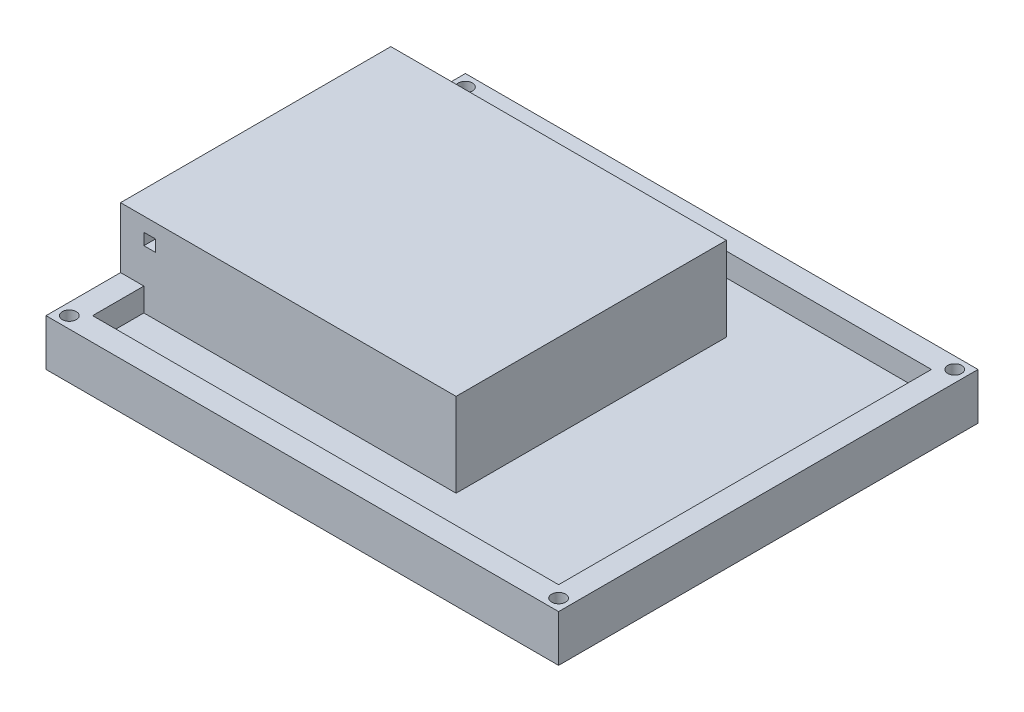
SolidWorks part; units mm, degrees
ref_plane "Front Plane" through (0, 0, 0) normal (0, 0, 1) x (1, 0, 0)
ref_plane "Top Plane" through (0, 0, 0) normal (0, 1, 0) x (1, 0, 0)
ref_plane "Right Plane" through (0, 0, 0) normal (1, 0, 0) x (0, 0, -1)
sketch "Sketch1" plane through (0, 0, 0) normal (0, 1, 0) x (1, 0, 0)
  line L1 (-55, -45) -> (55, -45)
  line L2 (-55, -45) -> (-55, 45)
  line L3 (-55, 45) -> (55, 45)
  line L4 (55, -45) -> (55, 45)
  line L5 (-55, -45) -> (55, 45) construction
  line L6 (-55, 45) -> (55, -45) construction
  point P0 (0, 0)
  dimension "D1" = 110
  dimension "D2" = 90
extrude "Boss-Extrude2" add sketch "Sketch1" along normal blind 5
sketch "Sketch2" plane through (0, 5, 0) normal (0, 1, 0) x (1, 0, 0)
  line L0 (-55, 45) -> (55, 45)
  line L1 (-55, 45) -> (-55, 40)
  line L2 (55, 45) -> (55, 40)
  line L3 (-55, 40) -> (55, 40)
  dimension "D1" = 5
extrude "Boss-Extrude4" add sketch "Sketch2" along normal blind 25
sketch "Sketch3" plane through (0, 5, 0) normal (0, 1, 0) x (1, 0, 0)
  line L0 (-55, -45) -> (55, -45)
  line L1 (-55, -45) -> (-55, -40)
  line L2 (55, -45) -> (55, -40)
  line L3 (-55, -40) -> (55, -40)
  dimension "D1" = 5
extrude "Boss-Extrude5" add sketch "Sketch3" along normal blind 25
sketch "Sketch5" plane through (0, 5, 0) normal (0, 1, 0) x (1, 0, 0)
  line L0 (55, 40) -> (55, -40)
  line L1 (55, 40) -> (50, 40)
  line L2 (55, -40) -> (50, -40)
  line L3 (50, 40) -> (50, -40)
  line L4 (55, -40) -> (55, 40) construction
  line L5 (55, 40) -> (55, 45) construction
  dimension "D1" = 5
extrude "Boss-Extrude6" add sketch "Sketch5" along normal blind 25
sketch "Sketch7" plane through (0, 5, 0) normal (0, 1, 0) x (1, 0, 0)
sketch "Sketch8" plane through (0, 5, 0) normal (0, 1, 0) x (1, 0, 0)
  line L0 (-55, 29) -> (17, 29)
  line L1 (-55, 40) -> (-55, -40) construction
  line L2 (17, 29) -> (17, -29)
  line L3 (17, -29) -> (-55, -29)
  line L4 (-55, -29) -> (-55, -40)
  line L5 (-55, 40) -> (-55, 29)
  line L6 (-55, 29) -> (17, 29)
  line L7 (-55, 29) -> (-55, -29)
  line L8 (17, 29) -> (17, -29)
  line L9 (-55, -29) -> (17, -29)
  line M3 (-55, 40) -> (-55, -40)
  dimension "D1" = 11
  dimension "D2" = 11
  dimension "D3" = 72
extrude "Boss-Extrude7" add sketch "Sketch8" along normal blind 25 contours L3 L2 L0 M3
sketch "Sketch10" plane through (-55, 0, 0) normal (-1, 0, 0) x (0, 0, 1)
  line L1 (-29, 5) -> (-29, 20.1155)
  line L2 (29, 5) -> (29, 20.1155)
  line L3 (-29, 20.1155) -> (29, 20.1155)
  line L4 (-29, 20.1155) -> (-29, 0)
  line L5 (-29, 20.1155) -> (-26, 20.1155)
  line L6 (-29, 0) -> (-26, 0)
  line L7 (-26, 20.1155) -> (-26, 0)
  line L8 (-45, 0) -> (45, 0) construction
  line L9 (29, 20.1155) -> (29, 0)
  line L10 (29, 20.1155) -> (26, 20.1155)
  line L11 (29, 0) -> (26, 0)
  line L12 (26, 20.1155) -> (26, 0)
  line L13 (-29, 20.1155) -> (29, 20.1155)
  line L14 (-29, 20.1155) -> (-29, 23.1155)
  line L15 (29, 20.1155) -> (29, 23.1155)
  line L16 (-29, 23.1155) -> (29, 23.1155)
  line L17 (-26, 20.1155) -> (26, 20.1155)
  line L18 (-26, 20.1155) -> (-26, 0)
  line L19 (26, 20.1155) -> (26, 0)
  line L20 (-26, 0) -> (26, 0)
  line M22 (-45, 0) -> (45, 0)
  dimension "D1" = 3
  dimension "D2" = 3
  dimension "D3" = 3
extrude "Cut-Extrude1" cut sketch "Sketch10" against normal blind 70 contours L12 L3 L7 M22
sketch "Sketch11" plane through (-55, 0, 0) normal (-1, 0, 0) x (0, 0, 1)
  line L0 (-45, 30) -> (45, 30)
  line L1 (-45, 30) -> (-45, 23)
  line L2 (45, 30) -> (45, 23)
  line L3 (-45, 23) -> (45, 23)
  dimension "D1" = 7
extrude "Cut-Extrude2" cut sketch "Sketch11" against normal blind 110
sketch "Sketch12" plane through (0, 23, 0) normal (0, 1, 0) x (1, 0, 0)
  circle A0 centre (52.5, -42.5) radius 1.5
extrude "Cut-Extrude3" cut sketch "Sketch12" against normal blind 23
sketch "Sketch13" plane through (0, 23, 0) normal (0, 1, 0) x (1, 0, 0)
  circle A0 centre (-52.5, -42.5) radius 1.5
extrude "Cut-Extrude4" cut sketch "Sketch13" against normal blind 23
sketch "Sketch14" plane through (0, 23, 0) normal (0, 1, 0) x (1, 0, 0)
  circle A0 centre (52.5, 42.5) radius 1.5
extrude "Cut-Extrude5" cut sketch "Sketch14" against normal blind 23
sketch "Sketch15" plane through (0, 23, 0) normal (0, 1, 0) x (1, 0, 0)
  circle A0 centre (-52.5, 42.5) radius 1.5
extrude "Cut-Extrude6" cut sketch "Sketch15" against normal blind 23
sketch "Sketch18" plane through (-55, 0, 0) normal (-1, 0, 0) x (0, 0, 1)
  line L0 (-45, 23) -> (-40, 23)
  line L1 (-45, 23) -> (-45, 10)
  line L2 (-40, 23) -> (-40, 10)
  line L3 (-45, 10) -> (-40, 10)
  dimension "D1" = 13
extrude "Cut-Extrude7" cut sketch "Sketch18" against normal blind 110
sketch "Sketch19" plane through (0, 0, -40) normal (0, 0, -1) x (-1, 0, 0)
  line L0 (-55, 23) -> (-50, 23)
  line L1 (-55, 23) -> (-55, 10)
  line L2 (-50, 23) -> (-50, 10)
  line L3 (-55, 10) -> (-50, 10)
  dimension "D1" = 13
extrude "Cut-Extrude13" cut sketch "Sketch19" against normal blind 85
sketch "Sketch26" plane through (50, 0, 0) normal (1, 0, 0) x (0, 0, -1)
  line L0 (-45, 10) -> (-40, 10)
  line L1 (-45, 10) -> (-45, 23)
  line L2 (-40, 10) -> (-40, 23)
  line L3 (-45, 23) -> (-40, 23)
  dimension "D1" = 13
extrude "Cut-Extrude17" cut sketch "Sketch26" against normal blind 105
sketch "Sketch29" plane through (0, 5, 0) normal (0, 1, 0) x (1, 0, 0)
  line L0 (-55, 40) -> (50, 40) construction
  line L1 (-50, 40) -> (-55, 40)
  line L2 (-50, 40) -> (-50, 29)
  line L3 (-50, 29) -> (-55, 29)
  line L4 (-55, 40) -> (-55, 29)
  dimension "D1" = 5
extrude "Boss-Extrude14" add sketch "Sketch29" along normal blind 5
sketch "Sketch30" plane through (0, 5, 0) normal (0, 1, 0) x (1, 0, 0)
  line L0 (17, -29) -> (-55, -29) construction
  line L1 (-50, -29) -> (-55, -29)
  line L2 (-50, -29) -> (-50, -40)
  line L3 (-50, -40) -> (-55, -40)
  line L4 (-55, -29) -> (-55, -40)
  dimension "D1" = 5
extrude "Boss-Extrude15" add sketch "Sketch30" along normal blind 5
sketch "Sketch34" plane through (0, 0, 29) normal (0, 0, 1) x (1, 0, 0)
  line L0 (-50, 10) -> (-55, 10)
  line L1 (-50, 10) -> (-50, 20)
  line L2 (-55, 10) -> (-55, 20)
  line L3 (-50, 20) -> (-55, 20)
  line L6 (-50, 20) -> (-47.5, 20)
  line L7 (-50, 20) -> (-50, 17.5)
  line L8 (-50, 17.5) -> (-47.5, 17.5)
  line L9 (-47.5, 20) -> (-47.5, 17.5)
  dimension "D1" = 10
  dimension "D2" = 2.5
  dimension "D3" = 2.5
extrude "Cut-Extrude18" cut sketch "Sketch34" against normal blind 3 contours L9 L6 L1 L8
sketch "Sketch37" plane through (0, 0, 29) normal (0, 0, 1) x (1, 0, 0)
  line L0 (-55, 23) -> (-55, 10)
  line L1 (-55, 23) -> (17, 23)
  line L2 (-55, 10) -> (17, 10)
  line L3 (17, 23) -> (17, 10)
  dimension "D1" = 72
extrude "Cut-Extrude20" cut sketch "Sketch37" against normal blind 58
sketch "Sketch39" plane through (0, 10, 0) normal (0, 1, 0) x (1, 0, 0)
  line L1 (17, 29) -> (-55, 29)
  line L2 (17, 29) -> (17, 26)
  line L3 (17, 26) -> (-55, 26)
  line L4 (-55, 29) -> (-55, 26)
extrude "Boss-Extrude17" add sketch "Sketch39" along normal blind 13
sketch "Sketch41" plane through (0, 10, 0) normal (0, 1, 0) x (1, 0, 0)
  line L1 (15, 26) -> (17, 26)
  line L2 (15, 26) -> (15, -29)
  line L3 (15, -29) -> (17, -29)
  line L4 (17, 26) -> (17, -29)
extrude "Boss-Extrude18" add sketch "Sketch41" along normal blind 13
sketch "Sketch43" plane through (0, 10, 0) normal (0, 1, 0) x (1, 0, 0)
  line L0 (-55, -45) -> (-55, -26) construction
  line L1 (15, -26) -> (-55, -26)
  line L2 (15, -26) -> (15, -29)
  line L3 (15, -29) -> (-55, -29)
  line L4 (-55, -26) -> (-55, -29)
extrude "Boss-Extrude19" add sketch "Sketch43" along normal blind 13
sketch "Sketch44" plane through (0, 23, 0) normal (0, 1, 0) x (1, 0, 0)
  line L0 (15, 26) -> (-55, 26)
  line L1 (15, 26) -> (15, -26)
  line L2 (-55, 26) -> (-55, -26)
  line L3 (15, -26) -> (-55, -26)
  dimension "D1" = 52
extrude "Boss-Extrude22" add sketch "Sketch44" against normal blind 3
sketch "Sketch53" plane through (0, 0, 29) normal (0, 0, 1) x (1, 0, 0)
  line L1 (-50, 10) -> (-55, 10)
  line L2 (-50, 10) -> (-50, 23)
  line L3 (-50, 23) -> (-55, 23)
  line L4 (-55, 10) -> (-55, 23)
sketch "Sketch55" plane through (0, 0, 29) normal (0, 0, 1) x (1, 0, 0)
  line L1 (-50, 23) -> (-47.5, 23)
  line L2 (-50, 23) -> (-50, 17.5)
  line L3 (-50, 17.5) -> (-47.5, 17.5)
  line L4 (-47.5, 23) -> (-47.5, 17.5)
  line L5 (-50, 17.5) -> (-47.5, 17.5)
  line L6 (-50, 17.5) -> (-50, 20)
  line L7 (-50, 20) -> (-47.5, 20)
  line L8 (-47.5, 17.5) -> (-47.5, 20)
  dimension "D1" = 2.5
  dimension "D2" = 5.5
  dimension "D3" = 2.5
extrude "Cut-Extrude25" cut sketch "Sketch55" against normal blind 3 contours L7 L2 L3 L4
